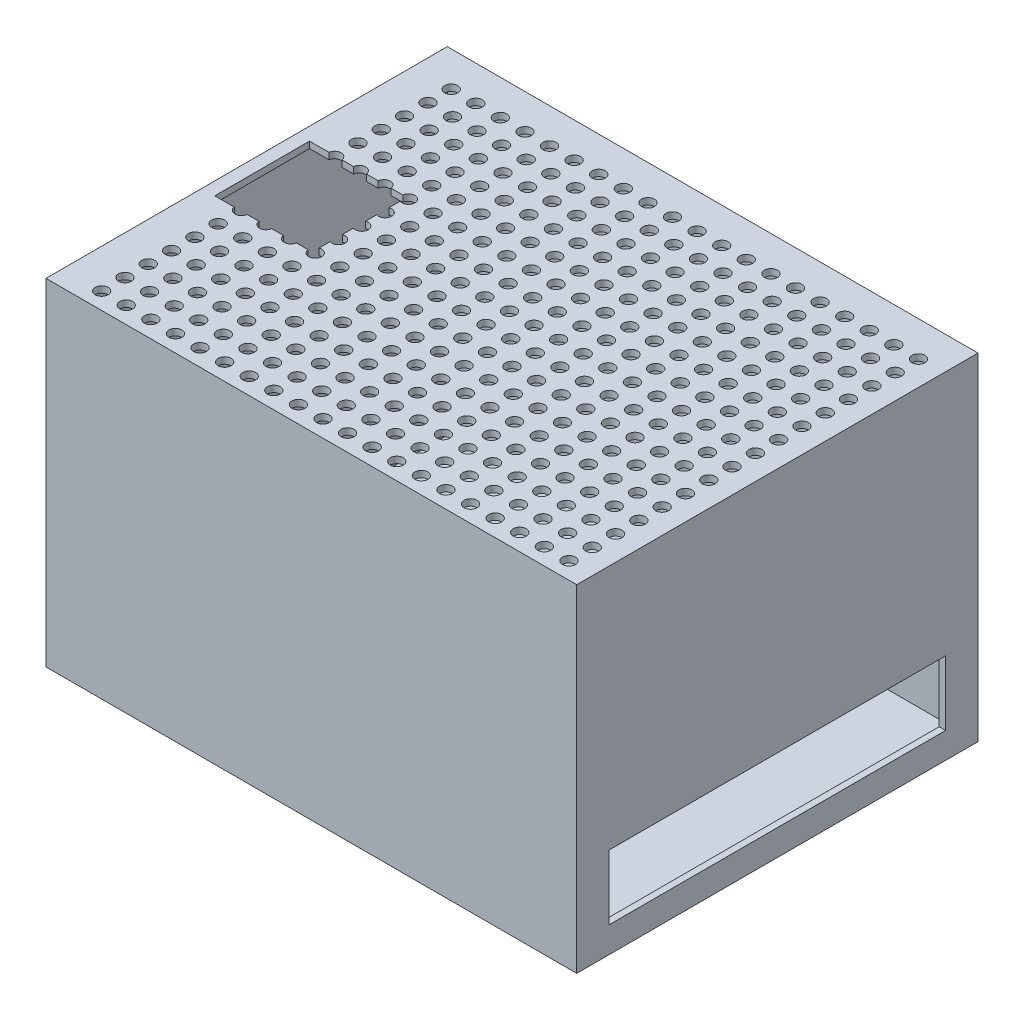
SolidWorks part; units mm, degrees
ref_plane "Front Plane" through (0, 0, 0) normal (0, 0, 1) x (1, 0, 0)
ref_plane "Top Plane" through (0, 0, 0) normal (0, 1, 0) x (1, 0, 0)
ref_plane "Right Plane" through (0, 0, 0) normal (1, 0, 0) x (0, 0, -1)
sketch "Sketch1" plane through (0, 0, 0) normal (0, 0, 1) x (1, 0, 0)
  line L0 (-5, 255) -> (405, 255)
  line L1 (0, 0) -> (400, 0)
  line L2 (0, 0) -> (0, 250)
  line L3 (0, 250) -> (400, 250)
  line L4 (400, 0) -> (400, 250)
  line L5 (405, -5) -> (405, 255)
  line L6 (-5, -5) -> (405, -5)
  line L7 (-5, -5) -> (-5, 255)
  dimension "D1" = 250
  dimension "D2" = 400
  dimension "D3" = 5
extrude "Boss-Extrude1" add sketch "Sketch1" along normal blind 300
sketch "Sketch2" plane through (0, 0, 300) normal (0, 0, 1) x (1, 0, 0)
  line L16 (-5, 255) -> (-5, -5)
  line L17 (-5, -5) -> (405, -5)
  line L18 (405, -5) -> (405, 255)
  line L19 (405, 255) -> (-5, 255)
extrude "Boss-Extrude2" add sketch "Sketch2" along normal blind 5
sketch "Sketch3" plane through (0, 0, 0) normal (0, 0, -1) x (-1, 0, 0)
  line L0 (-405, 255) -> (5, 255)
  line L1 (5, 255) -> (5, -5)
  line L2 (5, -5) -> (-405, -5)
  line L3 (-405, -5) -> (-405, 255)
extrude "Boss-Extrude3" add sketch "Sketch3" along normal blind 5
sketch "Sketch4" plane through (0, 255, 0) normal (0, 1, 0) x (1, 0, 0)
  line L0 (-5, 5) -> (25, 5)
  line L1 (-5, 5) -> (405, 5) construction
  circle A0 centre (25, -274) radius 5
  circle A1 centre (25, -246) radius 5
  circle A2 centre (25, -218) radius 5
  circle A3 centre (25, -190) radius 5
  circle A4 centre (25, -162) radius 5
  circle A5 centre (25, -134) radius 5
  circle A6 centre (25, -106) radius 5
  circle A7 centre (25, -78) radius 5
  circle A8 centre (25, -50) radius 5
  circle A9 centre (25, -22) radius 5
  circle A10 centre (44, -274) radius 5
  circle A11 centre (44, -246) radius 5
  circle A12 centre (44, -218) radius 5
  circle A13 centre (44, -190) radius 5
  circle A14 centre (44, -162) radius 5
  circle A15 centre (44, -134) radius 5
  circle A16 centre (44, -106) radius 5
  circle A17 centre (44, -78) radius 5
  circle A18 centre (44, -50) radius 5
  circle A19 centre (44, -22) radius 5
  circle A20 centre (63, -274) radius 5
  circle A21 centre (63, -246) radius 5
  circle A22 centre (63, -218) radius 5
  circle A23 centre (63, -190) radius 5
  circle A24 centre (63, -162) radius 5
  circle A25 centre (63, -134) radius 5
  circle A26 centre (63, -106) radius 5
  circle A27 centre (63, -78) radius 5
  circle A28 centre (63, -50) radius 5
  circle A29 centre (63, -22) radius 5
  circle A30 centre (82, -274) radius 5
  circle A31 centre (82, -246) radius 5
  circle A32 centre (82, -218) radius 5
  circle A33 centre (82, -190) radius 5
  circle A34 centre (82, -162) radius 5
  circle A35 centre (82, -134) radius 5
  circle A36 centre (82, -106) radius 5
  circle A37 centre (82, -78) radius 5
  circle A38 centre (82, -50) radius 5
  circle A39 centre (82, -22) radius 5
  circle A40 centre (101, -274) radius 5
  circle A41 centre (101, -246) radius 5
  circle A42 centre (101, -218) radius 5
  circle A43 centre (101, -190) radius 5
  circle A44 centre (101, -162) radius 5
  circle A45 centre (101, -134) radius 5
  circle A46 centre (101, -106) radius 5
  circle A47 centre (101, -78) radius 5
  circle A48 centre (101, -50) radius 5
  circle A49 centre (101, -22) radius 5
  circle A50 centre (120, -274) radius 5
  circle A51 centre (120, -246) radius 5
  circle A52 centre (120, -218) radius 5
  circle A53 centre (120, -190) radius 5
  circle A54 centre (120, -162) radius 5
  circle A55 centre (120, -134) radius 5
  circle A56 centre (120, -106) radius 5
  circle A57 centre (120, -78) radius 5
  circle A58 centre (120, -50) radius 5
  circle A59 centre (120, -22) radius 5
  circle A60 centre (139, -274) radius 5
  circle A61 centre (139, -246) radius 5
  circle A62 centre (139, -218) radius 5
  circle A63 centre (139, -190) radius 5
  circle A64 centre (139, -162) radius 5
  circle A65 centre (139, -134) radius 5
  circle A66 centre (139, -106) radius 5
  circle A67 centre (139, -78) radius 5
  circle A68 centre (139, -50) radius 5
  circle A69 centre (139, -22) radius 5
  circle A70 centre (158, -274) radius 5
  circle A71 centre (158, -246) radius 5
  circle A72 centre (158, -218) radius 5
  circle A73 centre (158, -190) radius 5
  circle A74 centre (158, -162) radius 5
  circle A75 centre (158, -134) radius 5
  circle A76 centre (158, -106) radius 5
  circle A77 centre (158, -78) radius 5
  circle A78 centre (158, -50) radius 5
  circle A79 centre (158, -22) radius 5
  circle A80 centre (177, -274) radius 5
  circle A81 centre (177, -246) radius 5
  circle A82 centre (177, -218) radius 5
  circle A83 centre (177, -190) radius 5
  circle A84 centre (177, -162) radius 5
  circle A85 centre (177, -134) radius 5
  circle A86 centre (177, -106) radius 5
  circle A87 centre (177, -78) radius 5
  circle A88 centre (177, -50) radius 5
  circle A89 centre (177, -22) radius 5
  circle A90 centre (196, -274) radius 5
  circle A91 centre (196, -246) radius 5
  circle A92 centre (196, -218) radius 5
  circle A93 centre (196, -190) radius 5
  circle A94 centre (196, -162) radius 5
  circle A95 centre (196, -134) radius 5
  circle A96 centre (196, -106) radius 5
  circle A97 centre (196, -78) radius 5
  circle A98 centre (196, -50) radius 5
  circle A99 centre (196, -22) radius 5
  circle A100 centre (215, -274) radius 5
  circle A101 centre (215, -246) radius 5
  circle A102 centre (215, -218) radius 5
  circle A103 centre (215, -190) radius 5
  circle A104 centre (215, -162) radius 5
  circle A105 centre (215, -134) radius 5
  circle A106 centre (215, -106) radius 5
  circle A107 centre (215, -78) radius 5
  circle A108 centre (215, -50) radius 5
  circle A109 centre (215, -22) radius 5
  circle A110 centre (234, -274) radius 5
  circle A111 centre (234, -246) radius 5
  circle A112 centre (234, -218) radius 5
  circle A113 centre (234, -190) radius 5
  circle A114 centre (234, -162) radius 5
  circle A115 centre (234, -134) radius 5
  circle A116 centre (234, -106) radius 5
  circle A117 centre (234, -78) radius 5
  circle A118 centre (234, -50) radius 5
  circle A119 centre (234, -22) radius 5
  circle A120 centre (253, -274) radius 5
  circle A121 centre (253, -246) radius 5
  circle A122 centre (253, -218) radius 5
  circle A123 centre (253, -190) radius 5
  circle A124 centre (253, -162) radius 5
  circle A125 centre (253, -134) radius 5
  circle A126 centre (253, -106) radius 5
  circle A127 centre (253, -78) radius 5
  circle A128 centre (253, -50) radius 5
  circle A129 centre (253, -22) radius 5
  circle A130 centre (272, -274) radius 5
  circle A131 centre (272, -246) radius 5
  circle A132 centre (272, -218) radius 5
  circle A133 centre (272, -190) radius 5
  circle A134 centre (272, -162) radius 5
  circle A135 centre (272, -134) radius 5
  circle A136 centre (272, -106) radius 5
  circle A137 centre (272, -78) radius 5
  circle A138 centre (272, -50) radius 5
  circle A139 centre (272, -22) radius 5
  circle A140 centre (291, -274) radius 5
  circle A141 centre (291, -246) radius 5
  circle A142 centre (291, -218) radius 5
  circle A143 centre (291, -190) radius 5
  circle A144 centre (291, -162) radius 5
  circle A145 centre (291, -134) radius 5
  circle A146 centre (291, -106) radius 5
  circle A147 centre (291, -78) radius 5
  circle A148 centre (291, -50) radius 5
  circle A149 centre (291, -22) radius 5
  circle A150 centre (310, -274) radius 5
  circle A151 centre (310, -246) radius 5
  circle A152 centre (310, -218) radius 5
  circle A153 centre (310, -190) radius 5
  circle A154 centre (310, -162) radius 5
  circle A155 centre (310, -134) radius 5
  circle A156 centre (310, -106) radius 5
  circle A157 centre (310, -78) radius 5
  circle A158 centre (310, -50) radius 5
  circle A159 centre (310, -22) radius 5
  circle A160 centre (329, -274) radius 5
  circle A161 centre (329, -246) radius 5
  circle A162 centre (329, -218) radius 5
  circle A163 centre (329, -190) radius 5
  circle A164 centre (329, -162) radius 5
  circle A165 centre (329, -134) radius 5
  circle A166 centre (329, -106) radius 5
  circle A167 centre (329, -78) radius 5
  circle A168 centre (329, -50) radius 5
  circle A169 centre (329, -22) radius 5
  circle A170 centre (348, -274) radius 5
  circle A171 centre (348, -246) radius 5
  circle A172 centre (348, -218) radius 5
  circle A173 centre (348, -190) radius 5
  circle A174 centre (348, -162) radius 5
  circle A175 centre (348, -134) radius 5
  circle A176 centre (348, -106) radius 5
  circle A177 centre (348, -78) radius 5
  circle A178 centre (348, -50) radius 5
  circle A179 centre (348, -22) radius 5
  circle A180 centre (367, -274) radius 5
  circle A181 centre (367, -246) radius 5
  circle A182 centre (367, -218) radius 5
  circle A183 centre (367, -190) radius 5
  circle A184 centre (367, -162) radius 5
  circle A185 centre (367, -134) radius 5
  circle A186 centre (367, -106) radius 5
  circle A187 centre (367, -78) radius 5
  circle A188 centre (367, -50) radius 5
  circle A189 centre (367, -22) radius 5
  circle A190 centre (386, -274) radius 5
  circle A191 centre (386, -246) radius 5
  circle A192 centre (386, -218) radius 5
  circle A193 centre (386, -190) radius 5
  circle A194 centre (386, -162) radius 5
  circle A195 centre (386, -134) radius 5
  circle A196 centre (386, -106) radius 5
  circle A197 centre (386, -78) radius 5
  circle A198 centre (386, -50) radius 5
  circle A199 centre (386, -22) radius 5
  point P6 (0, 0)
  point P406 (0, 0)
  dimension "D2" = 10
  dimension "D1" = 30
  dimension "D3" = 20
extrude "Cut-Extrude1" cut sketch "Sketch4" against normal blind 10 contours A19 | A29 | A39 | A49 | A59 | A69 | A9 | A79 | A89 | A99 | A109 | A119 | A129 | A139 | A149 | A159 | A169 | A179 | A189 | A199
pattern_linear "LPattern1" count 16 spacing 18 along (0, 0, 1) of "Cut-Extrude1"
sketch "Sketch5" plane through (0, 255, 0) normal (0, 1, 0) x (1, 0, 0)
  line L0 (5, -111.395) -> (5, -184.605)
  line L6 (-5, 5) -> (5, 5)
  line L7 (5, -184.605) -> (80.21, -184.605)
  line L8 (5, -111.395) -> (80.21, -111.395)
  line L9 (80.21, -111.395) -> (80.21, -184.605)
  line L10 (-5, 5) -> (405, 5) construction
  point P3 (5, -148)
  point P15 (42.605, -148)
extrude "Cut-Extrude2" cut sketch "Sketch5" against normal blind 10 contours L9 L8 L0 L7
sketch "Sketch8" plane through (405, 0, 0) normal (1, 0, 0) x (0, 0, -1)
  line L0 (-305, -5) -> (-305, 15)
  line L1 (-305, -5) -> (-305, 255) construction
  line L5 (-280, 65) -> (-20, 65)
  line L6 (-280, 65) -> (-280, 15)
  line L7 (-280, 15) -> (-20, 15)
  line L8 (-20, 15) -> (-20, 65)
  point P12 (-150, 65)
extrude "Cut-Extrude3" cut sketch "Sketch8" against normal blind 10 contours L7 L8 L5 L6
